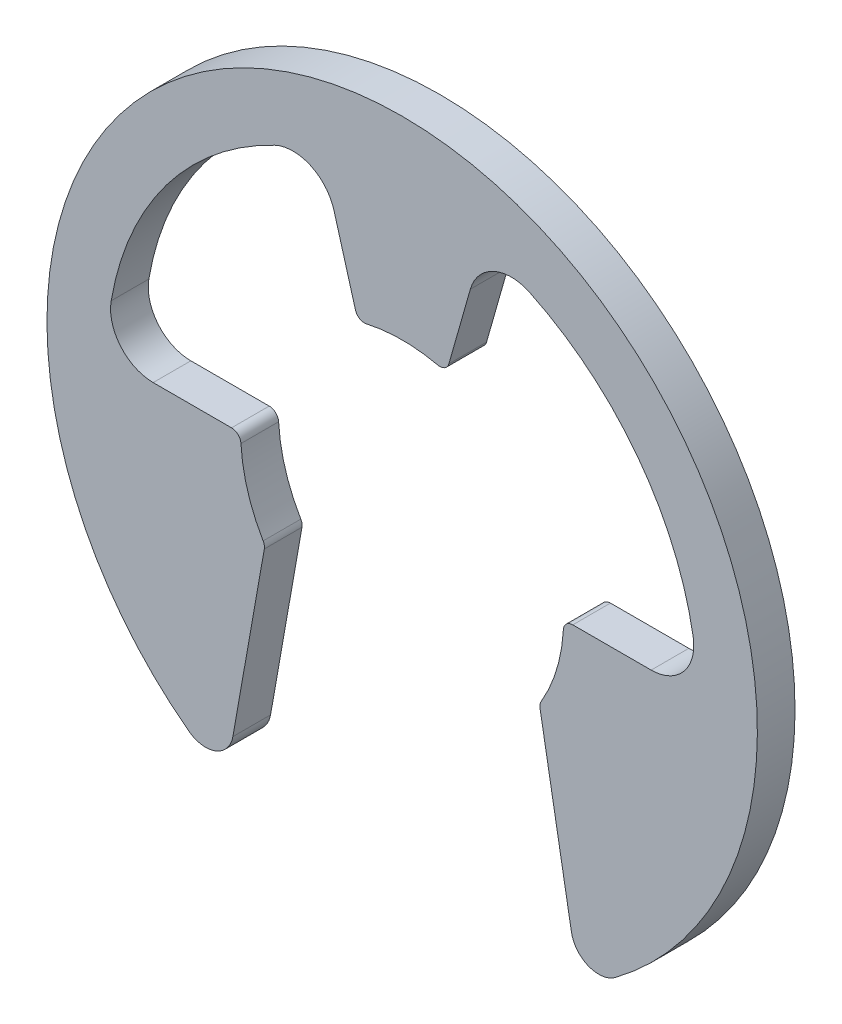
SolidWorks part; units mm, degrees
ref_plane "Front Plane" through (0, 0, 0) normal (0, 0, 1) x (1, 0, 0)
ref_plane "Top Plane" through (0, 0, 0) normal (0, 1, 0) x (1, 0, 0)
ref_plane "Right Plane" through (0, 0, 0) normal (1, 0, 0) x (0, 0, -1)
sketch "Sketch1" plane through (0, 0, 0) normal (0, 0, 1) x (1, 0, 0)
  circle A0 centre (0, 0) radius 8.382 construction
  circle A1 centre (0, 0) radius 3.81 construction
  point P3 (-8.382, 0)
  dimension "Ring OD" = 16.764
  dimension "ID" = 7.62
sketch "Sketch2" plane through (0, 0, 0) normal (0, 1, 0) x (1, 0, 0)
  line L0 (0, -0.4445) -> (0, 0.4445) construction
  line L1 (-8.382, -0.4445) -> (0, -0.4445) construction
  line L2 (-8.382, -0.4445) -> (-8.382, 0.4445) construction
  line L3 (-8.382, 0.4445) -> (0, 0.4445) construction
  point P2 (0, 0)
  dimension "Ring Thickness" = 0.889
sketch "Sketch3" plane through (0, 0, 0) normal (0, 1, 0) x (1, 0, 0)
  line L0 (-8.382, -0.4445) -> (-8.382, 0.4445)
  line L1 (0, 0.4445) -> (0, -0.4445)
  line L2 (-8.382, -0.4445) -> (0, -0.4445)
  line L3 (-8.382, 0.4445) -> (0, 0.4445)
revolve "Revolve1" add sketch "Sketch3" angle 360 about L1
sketch "Sketch4" plane through (0, 0, 0) normal (0, 0, 1) x (1, 0, 0)
  line L0 (1.0434, 3.6643) -> (1.908, 6.7005)
  line L1 (-1.0434, 3.6643) -> (-1.908, 6.7005)
  line L2 (-3.2385, -2.007) -> (-4.167, -7.2728)
  line L3 (3.2385, -2.007) -> (4.167, -7.2728)
  line L4 (-6.9669, 0) -> (-3.81, 0)
  line L5 (6.9669, 0) -> (3.81, 0)
  line L6 (-8.382, 0) -> (0, 0) construction
  line L7 (-1.0434, 3.6643) -> (1.0434, 3.6643) construction
  line L8 (3.81, 0) -> (3.2385, -2.007) construction
  circle A0 centre (0, 0) radius 8.382 construction
  arc A1 (-4.167, -7.2728) -> (4.167, -7.2728) centre (0, 0) ccw
  circle A2 centre (0, 0) radius 3.81 construction
  circle A3 centre (0, 0) radius 3.81 construction
  arc A4 (6.9669, 0) -> (1.908, 6.7005) centre (0, 0) ccw
  arc A5 (-1.0434, 3.6643) -> (1.0434, 3.6643) centre (0, 0) cw
  arc A6 (-3.81, 0) -> (-3.2385, -2.007) centre (0, 0) ccw
  arc A7 (3.81, 0) -> (3.2385, -2.007) centre (0, 0) cw
  arc A8 (-1.908, 6.7005) -> (-6.9669, 0) centre (0, 0) ccw
  point P7 (0, 3.81)
  dimension "D1" = 6.9669
  dimension "D5" = 20
  dimension "D2" = 6.477
extrude "Cut-Extrude1" cut sketch "Sketch4" against normal through all both and the other way through all
fillet "Fillet1" radius 1.0058 4 edges at (6.9669, 0, 0) (1.908, 6.7005, 0) (-1.908, 6.7005, 0) (-6.9669, 0, 0)
fillet "Fillet2" radius 0.6538 2 edges at (4.167, -7.2728, 0) (-4.167, -7.2728, 0)
fillet "Fillet3" radius 0.2223 6 edges at (3.2385, -2.007, 0) (3.81, 0, 0) (1.0434, 3.6643, 0) (-1.0434, 3.6643, 0) (-3.2385, -2.007, 0) (-3.81, 0, 0)
sketch "Sketch5" plane through (0, 0, 0) normal (0, 0, 1) x (1, 0, 0)
  arc A0 (-3.81, 0) -> (-3.2385, -2.007) centre (0, 0) ccw construction
  point P0 (-3.6643, -1.0434)
equation "\"D1@Sketch4\"=(\"Ring OD@Sketch1\"+\"ID@Sketch1\")/3.5"
equation "\"D1@Fillet1\"=\"Ring OD@Sketch1\"*.06"
equation "\"D1@Fillet2\"=\"D1@Fillet1\"*.65"
equation "\"D1@Fillet3\"=\"Ring Thickness@Sketch2\"*.25"
equation "\"D2@Sketch4\"=\"ID@Sketch1\"*.85"
